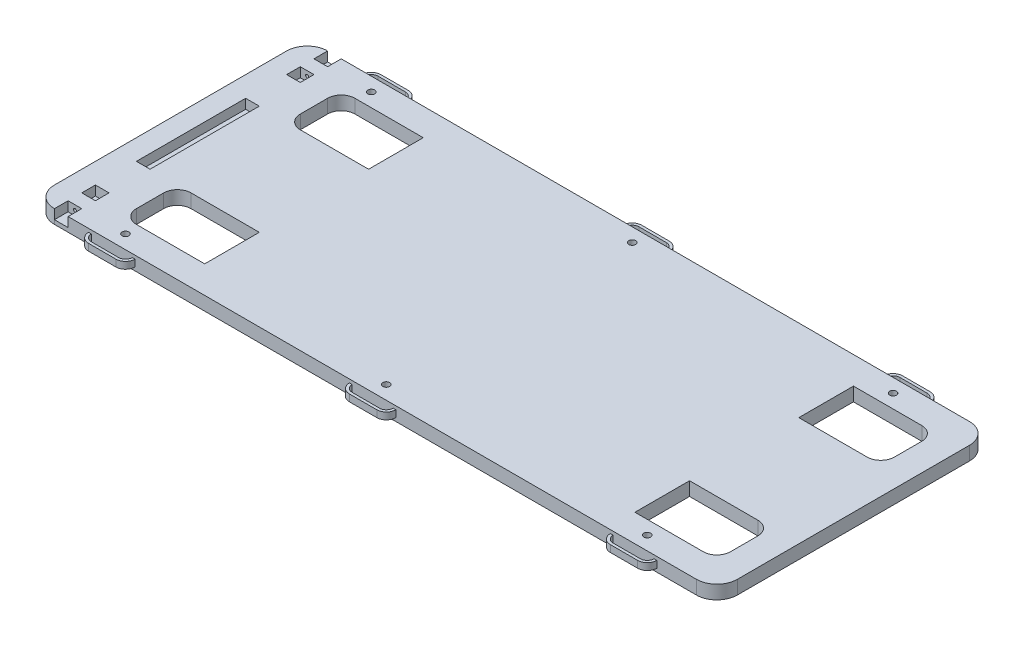
SolidWorks part; units mm, degrees
ref_plane "Front Plane" through (0, 0, 0) normal (0, 0, 1) x (1, 0, 0)
ref_plane "Top Plane" through (0, 0, 0) normal (0, 1, 0) x (1, 0, 0)
ref_plane "Right Plane" through (0, 0, 0) normal (1, 0, 0) x (0, 0, -1)
sketch "Main Body" plane through (0, 0, 0) normal (0, 1, 0) x (1, 0, 0)
  line L0 (-317.5, -107.95) -> (-317.5, 107.95)
  line L1 (-298.45, 127) -> (298.45, 127)
  line L2 (-298.45, -127) -> (298.45, -127)
  line L3 (317.5, 107.95) -> (317.5, -107.95)
  line L4 (-317.5, 0) -> (317.5, 0) construction
  arc A0 (-317.5, 107.95) -> (-298.45, 127) centre (-298.45, 107.95) cw
  arc A1 (-298.45, -127) -> (-317.5, -107.95) centre (-298.45, -107.95) cw
  arc A2 (298.45, 127) -> (317.5, 107.95) centre (298.45, 107.95) cw
  arc A3 (317.5, -107.95) -> (298.45, -127) centre (298.45, -107.95) cw
  point P14 (0, 0)
  dimension "D3" = 19.05
  dimension "D1" = 254
  dimension "D2" = 635
extrude "Boss-Extrude1" add sketch "Main Body" along normal blind 12.7
sketch "Sketch2" plane through (0, 0, 127) normal (0, 0, 1) x (1, 0, 0)
  line L0 (-298.45, 0) -> (298.45, 0) construction
  line L1 (-298.45, 12.7) -> (-260.35, 12.7)
  line L3 (-273.05, 0) -> (-260.35, 0)
sketch "Backrest Bracket Slot" plane through (0, 0, 127) normal (0, 0, 1) x (1, 0, 0)
  line L1 (-298.45, 12.7) -> (-285.75, 12.7)
  line L2 (-298.45, 12.7) -> (-298.45, 3.81)
  line L3 (-298.45, 3.81) -> (-285.75, 3.81)
  line L4 (-285.75, 12.7) -> (-285.75, 3.81)
  dimension "D1" = 12.7
  dimension "D2" = 8.89
extrude "Cut-Extrude3" cut sketch "Backrest Bracket Slot" against normal blind 12.7
sketch "Backrest Screw Hole" plane through (0, 0, 114.3) normal (0, 0, 1) x (1, 0, 0)
  line L0 (-298.45, 8.255) -> (-285.75, 8.255) construction
  line L1 (-298.45, 12.7) -> (-298.45, 3.81) construction
  line L2 (-285.75, 3.81) -> (-285.75, 12.7) construction
  circle A0 centre (-292.1, 8.255) radius 1.397
  dimension "D1" = 2.794
extrude "Cut-Extrude4" cut sketch "Backrest Screw Hole" against normal blind 6.35
mirror "Mirror1" about plane through (0, 0, 0) normal (0, 0, 1) of "Cut-Extrude4", "Cut-Extrude3"
sketch "Couch Foot Slits" plane through (0, 12.7, 0) normal (0, 1, 0) x (1, 0, 0)
  line L0 (-285.75, 114.3) -> (-285.75, -114.3) construction
  line L1 (-247.65, 101.6) -> (-184.15, 101.6)
  line L2 (-247.65, 50.8) -> (-184.15, 50.8)
  line L3 (-260.35, 88.9) -> (-260.35, 63.5)
  line L4 (292.1, 88.9) -> (292.1, 63.5)
  line L5 (-247.65, -50.8) -> (-184.15, -50.8)
  line L6 (-247.65, -101.6) -> (-184.15, -101.6)
  line L7 (-260.35, -63.5) -> (-260.35, -88.9)
  line L8 (292.1, -63.5) -> (292.1, -88.9)
  line L9 (317.5, -107.95) -> (317.5, 107.95) construction
  line L10 (298.45, 127) -> (-285.75, 127) construction
  line L12 (-285.75, -127) -> (298.45, -127) construction
  line L14 (215.9, 101.6) -> (279.4, 101.6)
  line L16 (-184.15, 101.6) -> (-184.15, 50.8)
  line L18 (215.9, 101.6) -> (215.9, 50.8)
  line L20 (-184.15, -50.8) -> (-184.15, -101.6)
  line L22 (215.9, -50.8) -> (215.9, -101.6)
  line L23 (215.9, 50.8) -> (279.4, 50.8)
  line L24 (215.9, -50.8) -> (279.4, -50.8)
  line L25 (215.9, -101.6) -> (279.4, -101.6)
  arc A0 (-260.35, 88.9) -> (-247.65, 101.6) centre (-247.65, 88.9) cw
  arc A1 (-247.65, 50.8) -> (-260.35, 63.5) centre (-247.65, 63.5) cw
  arc A2 (279.4, 101.6) -> (292.1, 88.9) centre (279.4, 88.9) cw
  arc A3 (292.1, 63.5) -> (279.4, 50.8) centre (279.4, 63.5) cw
  arc A4 (-260.35, -63.5) -> (-247.65, -50.8) centre (-247.65, -63.5) cw
  arc A5 (-247.65, -101.6) -> (-260.35, -88.9) centre (-247.65, -88.9) cw
  arc A6 (279.4, -50.8) -> (292.1, -63.5) centre (279.4, -63.5) cw
  arc A7 (292.1, -88.9) -> (279.4, -101.6) centre (279.4, -88.9) cw
  dimension "D6" = 12.7
  dimension "D9" = 12.7
  dimension "D1" = 25.4
  dimension "D2" = 25.4
  dimension "D3" = 25.4
  dimension "D4" = 25.4
  dimension "D5" = 101.6
  dimension "D7" = 76.2
  dimension "D8" = 76.2
extrude "Cut-Extrude5" cut sketch "Couch Foot Slits" against normal blind 25.4
ref_plane "Central Plane" through (0, 6.35, 0) normal (0, 1, 0) x (1, 0, 0)
sketch "Sketch24" plane through (0, 6.35, 0) normal (0, 1, 0) x (1, 0, 0)
  line L0 (-285.75, -127) -> (298.45, -127) construction
  line L1 (-15.24, -133.35) -> (10.16, -133.35)
  line L2 (-264.16, -127) -> (-264.16, -101.5898) construction
  line L3 (-257.81, -133.35) -> (-232.41, -133.35)
  line L5 (-257.81, -135.89) -> (-232.41, -135.89)
  line L7 (-266.7, -127) -> (-264.16, -127)
  line L8 (-226.06, -127) -> (-223.52, -127)
  line L9 (16.51, -127) -> (19.05, -127)
  line L10 (-15.24, -135.89) -> (10.16, -135.89)
  line L11 (-24.13, -127) -> (-21.59, -127)
  line L12 (227.33, -133.35) -> (252.73, -133.35)
  line L13 (259.08, -127) -> (261.62, -127)
  line L14 (227.33, -135.89) -> (252.73, -135.89)
  line L15 (218.44, -127) -> (220.98, -127)
  line L16 (-257.81, -133.35) -> (-15.24, -133.35) construction
  arc A0 (-257.81, -133.35) -> (-264.16, -127) centre (-257.81, -127) cw
  arc A1 (-257.81, -135.89) -> (-266.7, -127) centre (-257.81, -127) cw
  arc A2 (-232.41, -135.89) -> (-223.52, -127) centre (-232.41, -127) ccw
  arc A3 (-232.41, -133.35) -> (-226.06, -127) centre (-232.41, -127) ccw
  arc A4 (10.16, -133.35) -> (16.51, -127) centre (10.16, -127) ccw
  arc A5 (10.16, -135.89) -> (19.05, -127) centre (10.16, -127) ccw
  arc A6 (-15.24, -135.89) -> (-24.13, -127) centre (-15.24, -127) cw
  arc A7 (-15.24, -133.35) -> (-21.59, -127) centre (-15.24, -127) cw
  arc A8 (252.73, -133.35) -> (259.08, -127) centre (252.73, -127) ccw
  arc A9 (252.73, -135.89) -> (261.62, -127) centre (252.73, -127) ccw
  arc A10 (227.33, -135.89) -> (218.44, -127) centre (227.33, -127) cw
  arc A11 (227.33, -133.35) -> (220.98, -127) centre (227.33, -127) cw
  dimension "D2" = 2.54
  dimension "D1" = 2.54
  dimension "D3" = 38.1
  dimension "D4" = 25.4
  dimension "D5" = 19.05
  dimension "D7" = 242.57
  dimension "D6" = 3
extrude "Boss-Extrude2" add sketch "Sketch24" along normal mid plane 6.35
mirror "Mirror2" about plane through (0, 0, 0) normal (0, 0, 1) of "Boss-Extrude2"
sketch "Sketch37" plane through (0, 12.7, 0) normal (0, 1, 0) x (1, 0, 0)
  line L0 (-298.45, 114.3) -> (-298.45, 127) construction
  line L1 (-298.45, 50.8) -> (-285.75, 50.8)
  line L2 (-298.45, 50.8) -> (-298.45, -50.8)
  line L3 (-298.45, -50.8) -> (-285.75, -50.8)
  line L4 (-285.75, 50.8) -> (-285.75, -50.8)
  line L5 (-285.75, 114.3) -> (-285.75, 127) construction
  line L6 (-292.1, 114.3) -> (-290.703, -114.3) construction
  line L7 (-285.75, 114.3) -> (-298.45, 114.3) construction
  point P13 (-285.75, 0)
  point P14 (-291.4015, 0)
  dimension "D1" = 101.6
extrude "Cut-Extrude7" cut sketch "Sketch37" against normal blind 8.89
sketch "Sketch38" plane through (0, 12.7, 0) normal (0, 1, 0) x (1, 0, 0)
  line L0 (-266.7, -127) -> (-223.52, -127) construction
  line L1 (-221.2987, -101.6) -> (-221.2987, -127) construction
  line L2 (-247.65, -101.6) -> (-184.15, -101.6) construction
  line L3 (-21.59, -127) -> (16.51, -127) construction
  line L4 (220.98, -127) -> (259.08, -127) construction
  circle A0 centre (-245.11, -114.3) radius 3.175
  circle A1 centre (-2.54, -114.3) radius 3.175
  circle A2 centre (240.03, -114.3) radius 3.175
  point P6 (-245.11, -127)
  point P11 (-221.2987, -114.3)
  point P18 (-2.54, -127)
  point P25 (240.03, -127)
  dimension "D1" = 6.35
extrude "Cut-Extrude8" cut sketch "Sketch38" against normal up to next (12.7 mm away)
mirror "Mirror3" about plane through (0, 0, 0) normal (0, 0, 1) of "Cut-Extrude8"
sketch "Sketch39" plane through (0, 12.7, 0) normal (0, 1, 0) x (1, 0, 0)
  line L0 (-298.45, -114.3) -> (-298.45, -127) construction
  line L1 (-298.45, -101.6) -> (-285.75, -101.6)
  line L2 (-298.45, -101.6) -> (-298.45, -88.9)
  line L3 (-298.45, -88.9) -> (-285.75, -88.9)
  line L4 (-285.75, -101.6) -> (-285.75, -88.9)
  line L5 (-285.75, -114.3) -> (-285.75, -127) construction
  line L6 (-285.75, -114.3) -> (-298.45, -114.3) construction
  dimension "D1" = 12.7
extrude "Cut-Extrude9" cut sketch "Sketch39" against normal up to surface (8.89 mm away) up to face at (-292.1, 3.81, 120.65)
sketch "Sketch40" plane through (0, 0, 114.3) normal (0, 0, 1) x (1, 0, 0)
  circle A0 centre (-292.1, 8.255) radius 1.397
  circle A1 centre (-292.1, 8.255) radius 1.397 construction
extrude "Cut-Extrude10" cut sketch "Sketch40" against normal up to next
mirror "Mirror5" about plane through (0, 0, 0) normal (0, 0, 1) of "Cut-Extrude9", "Cut-Extrude10"
equation "\"0.4n\"=0.5"
